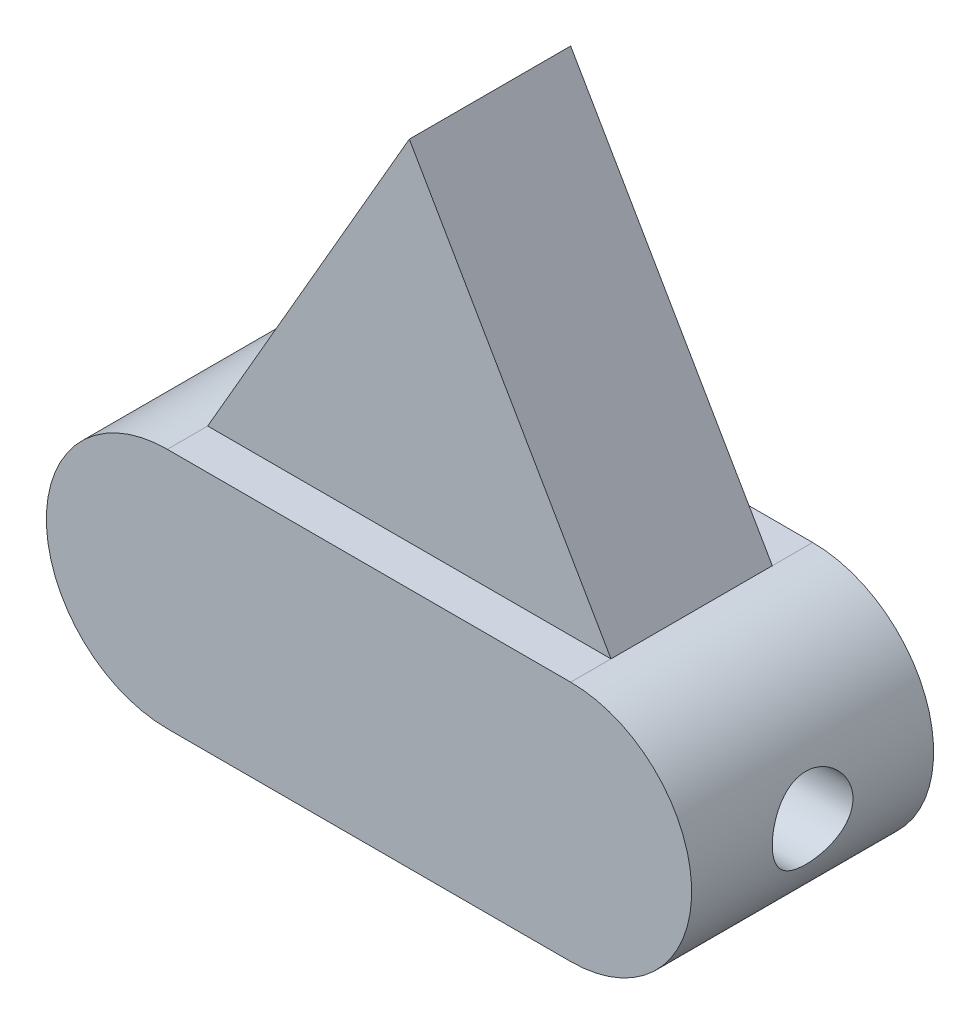
SolidWorks part; units mm, degrees
ref_plane "Front Plane" through (0, 0, 0) normal (0, 0, 1) x (1, 0, 0)
ref_plane "Top Plane" through (0, 0, 0) normal (0, 1, 0) x (1, 0, 0)
ref_plane "Right Plane" through (0, 0, 0) normal (1, 0, 0) x (0, 0, -1)
sketch "Sketch1" plane through (0, 0, 0) normal (0, 1, 0) x (1, 0, 0)
  line L0 (-63.5, 0) -> (63.5, 0) construction
  line L3 (-63.5, -25.4) -> (63.5, -25.4)
  arc A0 (-63.5, 25.4) -> (-63.5, -25.4) centre (-63.5, 0) ccw
  arc A1 (63.5, -25.4) -> (63.5, 25.4) centre (63.5, 0) ccw
  point P5 (0, 0)
  dimension "D2" = 25.4
  dimension "D1" = 127
sketch "Sketch2" plane through (0, 0, 0) normal (0, 1, 0) x (1, 0, 0)
  line L0 (-25.4, 43.9941) -> (-25.4, -43.9941) construction
  line L1 (-47.752, 75.8453) -> (-47.752, -49924.1547) construction
  arc A0 (47.2281, 18.7121) -> (-25.4, 43.9941) centre (0, 0) ccw
  arc A1 (47.2281, 18.7121) -> (47.2281, -18.7121) centre (50.8, 0) ccw
  arc A2 (-25.4, -43.9941) -> (47.2281, -18.7121) centre (0, 0) ccw
  arc A3 (-25.4, -43.9941) -> (-98.0281, -18.7121) centre (-50.8, 0) cw
  arc A4 (-98.0281, 18.7121) -> (-98.0281, -18.7121) centre (-101.6, 0) cw
  arc A5 (-98.0281, 18.7121) -> (-25.4, 43.9941) centre (-50.8, 0) cw
  point P13 (0, 0)
  point P14 (-25.4, 43.9941)
  dimension "D1" = 101.6
  dimension "D2" = 38.1
  dimension "D3" = 25.4
  dimension "D4" = 22.352
sketch "Sketch3" plane through (0, 0, 0) normal (0, 1, 0) x (1, 0, 0)
  line L1 (-63.5, 38.1) -> (63.5, 38.1)
  line L2 (-63.5, 38.1) -> (-63.5, -38.1)
  line L3 (-63.5, -38.1) -> (63.5, -38.1)
  line L4 (63.5, 38.1) -> (63.5, -38.1)
  line L5 (-63.5, 38.1) -> (63.5, -38.1) construction
  line L6 (-63.5, -38.1) -> (63.5, 38.1) construction
  point P0 (0, 0)
  dimension "D1" = 76.2
  dimension "D2" = 127
extrude "Boss-Extrude1" add sketch "Sketch3" along normal blind 76.2
sketch "Sketch4" plane through (0, 0, 38.1) normal (0, 0, 1) x (1, 0, 0)
  line L0 (-63.5, 76.2) -> (-63.5, 0) construction
  line L1 (63.5, 76.2) -> (63.5, 0) construction
  line L2 (-63.5, 76.2) -> (-63.5, 0)
  line L3 (63.5, 76.2) -> (63.5, 0)
  arc A0 (-63.5, 0) -> (-63.5, 76.2) centre (-63.5, 38.1) cw
  arc A1 (63.5, 76.2) -> (63.5, 0) centre (63.5, 38.1) cw
extrude "Boss-Extrude2" add sketch "Sketch4" against normal up to surface (76.2 mm away) up to face at (0, 38.1, -38.1)
sketch "Sketch5" plane through (0, 0, 0) normal (0, 0, 1) x (1, 0, 0)
  line L0 (-63.5, 76.2) -> (63.5, 76.2)
  line L1 (63.5, 76.2) -> (0, 186.1852)
  line L2 (0, 186.1852) -> (-63.5, 76.2)
extrude "Boss-Extrude3" add sketch "Sketch5" along normal mid plane 50.8
sketch "Sketch6" plane through (0, 0, 0) normal (1, 0, 0) x (0, 0, -1)
  circle A0 centre (0, 38.1) radius 12.7
  point P2 (0, 0)
  dimension "D1" = 25.4
  dimension "D2" = 38.1
extrude "Cut-Extrude1" cut sketch "Sketch6" against normal through all both and the other way through all
